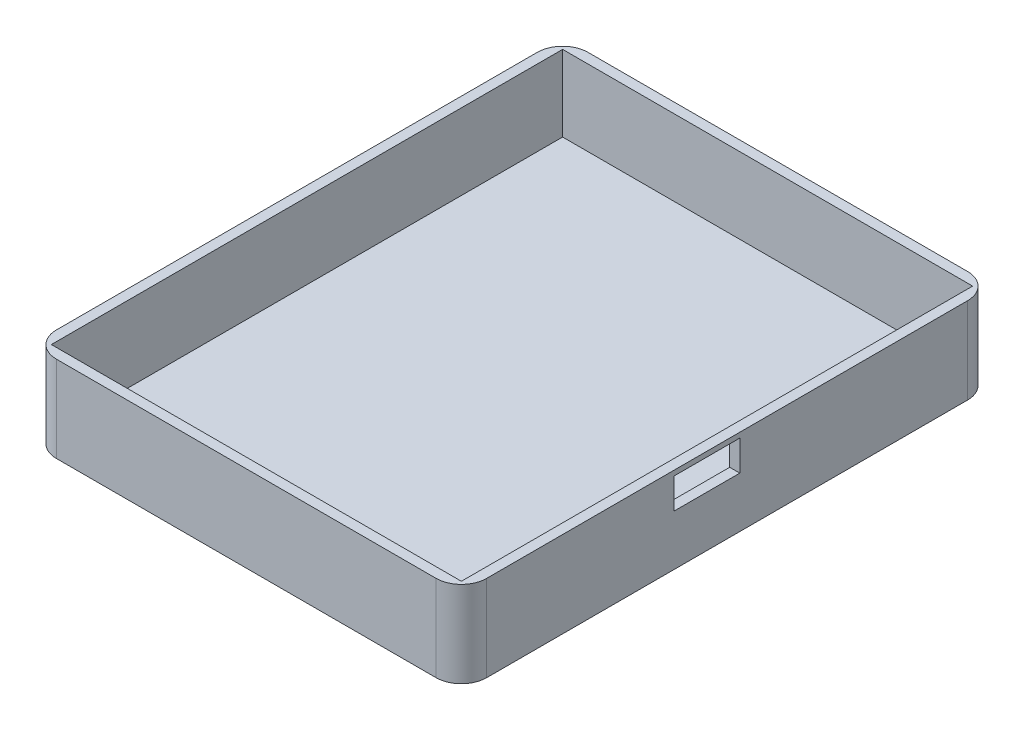
SolidWorks part; units mm, degrees
ref_plane "Front Plane" through (0, 0, 0) normal (0, 0, 1) x (1, 0, 0)
ref_plane "Top Plane" through (0, 0, 0) normal (0, 1, 0) x (1, 0, 0)
ref_plane "Right Plane" through (0, 0, 0) normal (1, 0, 0) x (0, 0, -1)
sketch "Sketch1" plane through (0, 0, 0) normal (0, 1, 0) x (1, 0, 0)
  line L1 (-42.5, -52.5) -> (42.5, -52.5)
  line L2 (-42.5, -52.5) -> (-42.5, 52.5)
  line L3 (-42.5, 52.5) -> (42.5, 52.5)
  line L4 (42.5, -52.5) -> (42.5, 52.5)
  line L5 (-42.5, -52.5) -> (42.5, 52.5) construction
  line L6 (-42.5, 52.5) -> (42.5, -52.5) construction
  point P0 (0, 0)
  dimension "D1" = 85
  dimension "D2" = 105
extrude "Boss-Extrude1" add sketch "Sketch1" along normal blind 17
shell "Shell1" thickness 2
sketch "Sketch3" plane through (42.5, 0, 0) normal (1, 0, 0) x (0, 0, -1)
  line L0 (-52.5, 17) -> (-52.5, 0) construction
  line L1 (-10.5, 10) -> (2.5, 10)
  line L2 (-10.5, 10) -> (-10.5, 16)
  line L3 (-10.5, 16) -> (2.5, 16)
  line L4 (2.5, 10) -> (2.5, 16)
  line L5 (-10.5, 10) -> (2.5, 16) construction
  line L6 (-10.5, 16) -> (2.5, 10) construction
  line L7 (52.5, 17) -> (52.5, 0) construction
  line L8 (-52.5, 17) -> (52.5, 17) construction
  point P0 (-4, 13)
  dimension "D1" = 42
  dimension "D2" = 50
  dimension "D3" = 10
  dimension "D4" = 1
extrude "Cut-Extrude1" cut sketch "Sketch3" against normal blind 10
fillet "Fillet1" radius 5 4 edges at (-42.5, 8.5, -52.5) (42.5, 8.5, -52.5) (42.5, 8.5, 52.5) (-42.5, 8.5, 52.5)
